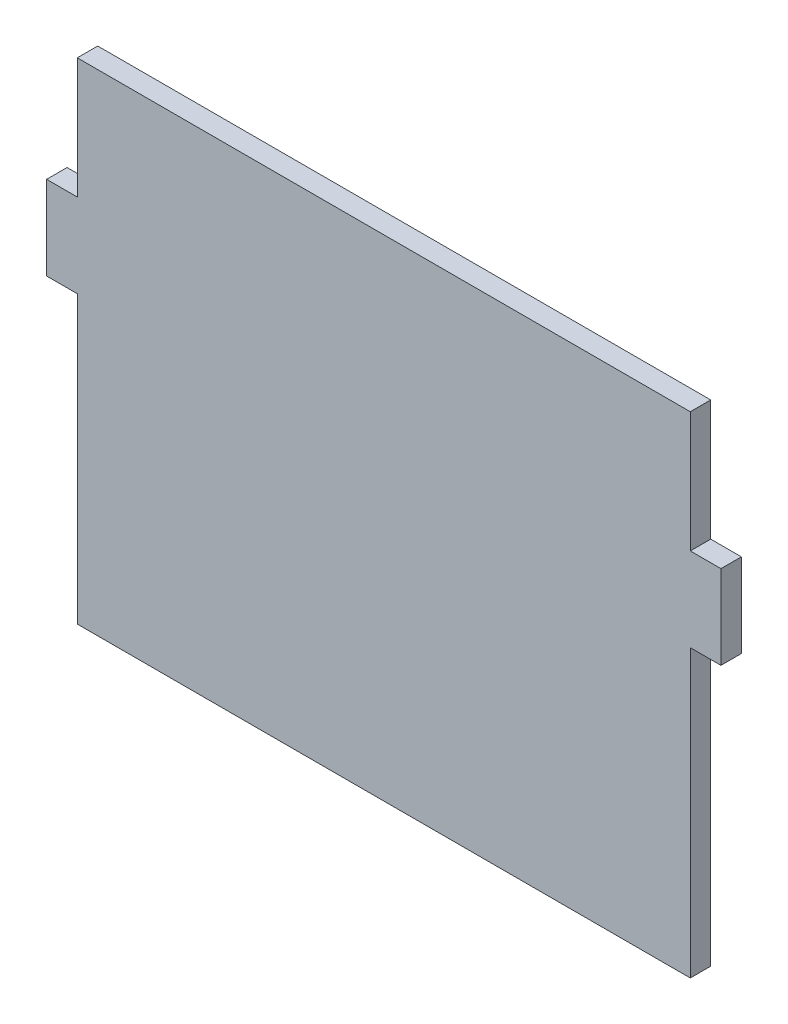
SolidWorks part; units mm, degrees
ref_plane "Ön Düzlem" through (0, 0, 0) normal (0, 0, 1) x (1, 0, 0)
ref_plane "Üst Düzlem" through (0, 0, 0) normal (0, 1, 0) x (1, 0, 0)
ref_plane "Sağ Düzlem" through (0, 0, 0) normal (1, 0, 0) x (0, 0, -1)
sketch "Çizim1" plane through (0, 0, 0) normal (0, 0, 1) x (1, 0, 0)
  line L0 (-150, -120) -> (-150, 20)
  line L1 (-150, -120) -> (150, -120) construction
  line L2 (-150, -120) -> (-150, 120) construction
  line L3 (-150, 120) -> (150, 120) construction
  line L4 (150, -120) -> (150, 120) construction
  line L5 (-150, -120) -> (150, 120) construction
  line L6 (-150, 120) -> (150, -120) construction
  line L7 (-150, 20) -> (-165, 20)
  line L8 (-165, 20) -> (-165, 61)
  line L9 (-165, 61) -> (-150, 61)
  line L10 (-150, 61) -> (-150, 120)
  line L11 (-150, 120) -> (150, 120)
  line L12 (150, 120) -> (150, 61)
  line L13 (150, 61) -> (165, 61)
  line L14 (165, 61) -> (165, 20)
  line L15 (165, 20) -> (150, 20)
  line L16 (150, 20) -> (150, -120)
  line L17 (150, -120) -> (-150, -120)
  point P0 (0, 0)
  dimension "D1" = 240
  dimension "D2" = 300
  dimension "D3" = 59
  dimension "D4" = 41
  dimension "D5" = 15
extrude "Yükseklik-Ekstrüzyon1" add sketch "Çizim1" along normal blind 10
